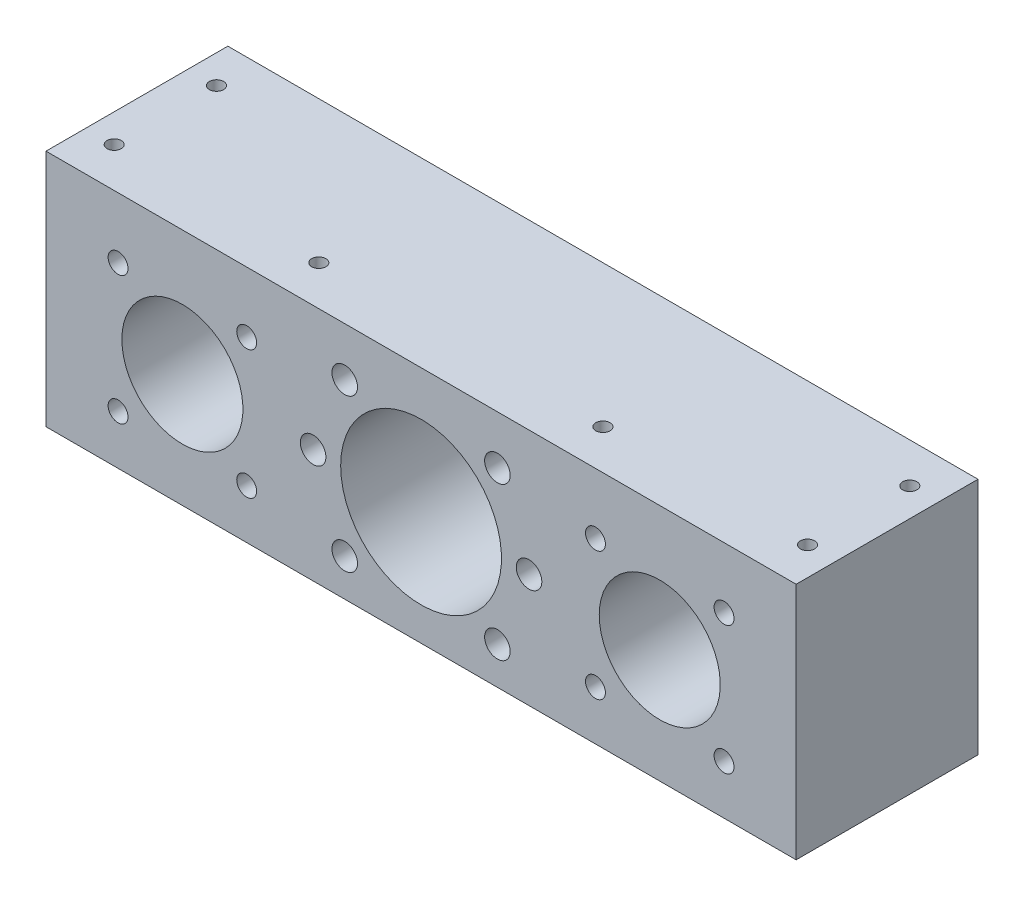
SolidWorks part; units mm, degrees
ref_plane "前视基准面" through (0, 0, 0) normal (0, 0, 1) x (1, 0, 0)
ref_plane "上视基准面" through (0, 0, 0) normal (0, 1, 0) x (1, 0, 0)
ref_plane "右视基准面" through (0, 0, 0) normal (1, 0, 0) x (0, 0, -1)
sketch "草图1" plane through (0, 0, 0) normal (0, 0, 1) x (1, 0, 0)
  line L1 (-66, 22) -> (66, 22)
  line L2 (-66, 22) -> (-66, -20)
  line L3 (-66, -20) -> (66, -20)
  line L4 (66, 22) -> (66, -20)
  dimension "D1" = 42
  dimension "D2" = 132
  dimension "D3" = 66
  dimension "D4" = 22
extrude "凸台-拉伸1" add sketch "草图1" along normal blind 32
sketch "草图2" plane through (0, 0, 0) normal (0, 0, -1) x (-1, 0, 0)
  circle A0 centre (0, 0) radius 14.15
  dimension "D1" = 28.3
extrude "切除-拉伸1" cut sketch "草图2" against normal blind 32
sketch "草图3" plane through (0, 0, 0) normal (0, 0, -1) x (-1, 0, 0)
  circle A0 centre (-42, 0) radius 10.65
  circle A1 centre (42, 0) radius 10.65
  dimension "D1" = 21.3
  dimension "D2" = 21.3
  dimension "D3" = 42
  dimension "D4" = 42
extrude "切除-拉伸2" cut sketch "草图3" against normal blind 32
sketch "草图6" plane through (0, 0, 32) normal (0, 0, 1) x (1, 0, 0)
  line L0 (25.1918, 8.3272) -> (27.1146, 8.7921)
  line L1 (27.1146, 8.7921) -> (27.6978, 8.9182)
  line L2 (27.6978, 8.9182) -> (28.2849, 9.0955)
  line L3 (28.2849, 9.0955) -> (28.8996, 9.328)
  line L4 (28.8996, 9.328) -> (29.1478, 9.4265)
  line L5 (29.1478, 9.4265) -> (29.8177, 9.659)
  line L6 (29.8177, 9.659) -> (30.2984, 9.328)
  line L7 (30.2984, 9.328) -> (30.8303, 8.8276)
  line L8 (30.59, 7.7716) -> (28.0209, 7.4603)
  line L9 (28.0209, 7.4603) -> (24.8095, 6.9875)
  line L10 (24.8095, 6.9875) -> (20.4003, 6.3097)
  line L11 (20.4003, 6.3097) -> (19.3207, 6.1285)
  line L12 (19.3207, 6.1285) -> (18.4696, 5.9472)
  line L13 (18.4696, 5.9472) -> (17.8707, 5.8172)
  line L14 (17.8707, 5.8172) -> (17.4924, 5.7344)
  line L15 (17.4924, 5.7344) -> (16.4009, 5.4035)
  line L16 (15.8414, 5.7226) -> (15.2976, 6.2427)
  line L17 (15.1006, 7.0544) -> (17.1299, 7.279)
  line L18 (17.1299, 7.279) -> (20.9677, 7.8267)
  line L19 (20.9677, 7.8267) -> (21.1336, 7.8433)
  line L20 (22.0543, 7.9656) -> (22.3508, 8.0119)
  line L21 (22.3508, 8.0119) -> (23.8757, 8.2484)
  line L22 (25.5858, 13.225) -> (25.6449, 14.0249)
  line L23 (25.6449, 14.0249) -> (26.4408, 14.2534)
  line L24 (26.4408, 14.2534) -> (27.489, 11.7513)
  line L25 (19.0409, 3.7879) -> (21.6061, 4.4302)
  line L26 (21.6061, 4.4302) -> (21.8661, 5.037)
  line L27 (22.9103, 5.0725) -> (23.4186, 4.4381)
  line L28 (23.6353, 3.7091) -> (23.2255, 3.1851)
  line L29 (23.1783, 2.2827) -> (23.1783, -5.9171)
  line L30 (21.5076, -10.8346) -> (21.1175, -10.0544)
  line L31 (21.1175, -10.0544) -> (20.5461, -9.0181)
  line L32 (20.5461, -9.0181) -> (19.3956, -6.9376)
  line L33 (19.3956, -6.9376) -> (19.829, -6.3938)
  line L34 (19.829, -6.3938) -> (21.6218, -8.1591)
  line L35 (21.7203, -6.3584) -> (21.7203, -3.4525)
  line L36 (21.7203, 3.126) -> (19.2892, 2.5388)
  line L37 (19.2892, 2.5388) -> (19.2892, 0.5214)
  line L38 (21.0032, 1.1755) -> (21.7203, 0.5627)
  line L39 (21.212, -0.373) -> (20.684, -0.4361)
  line L40 (20.684, -0.4361) -> (19.2892, -0.7316)
  line L41 (19.2892, -0.7316) -> (19.2892, -2.6111)
  line L42 (21.0465, -1.9571) -> (21.7203, -2.5391)
  line L43 (21.3066, -3.5332) -> (20.6131, -3.6356)
  line L44 (20.6131, -3.6356) -> (20.0221, -3.742)
  line L45 (20.0221, -3.742) -> (19.2892, -3.872)
  line L46 (19.2892, -3.872) -> (19.2852, -8.1394)
  line L47 (19.2852, -8.1394) -> (19.2576, -9.6604)
  line L48 (19.2576, -9.6604) -> (19.2025, -10.6809)
  line L49 (18.0322, -11.1892) -> (17.7918, -10.6809)
  line L50 (17.7918, -10.6809) -> (17.5357, -10.015)
  line L51 (17.8273, -5.5782) -> (17.8273, 1.9675)
  line L52 (17.7761, 3.654) -> (17.6736, 4.2489)
  line L53 (17.6736, 4.2489) -> (17.5673, 5.1473)
  line L54 (17.5673, 5.1473) -> (18.4105, 5.431)
  line L55 (18.4105, 5.431) -> (19.0409, 3.7879)
  line L56 (19.5847, 13.2092) -> (20.4437, 12.5197)
  line L57 (20.4437, 12.5197) -> (20.9441, 11.9404)
  line L58 (20.9441, 11.9404) -> (21.4169, 11.3651)
  line L59 (21.4169, 11.3651) -> (22.0001, 10.6559)
  line L60 (22.3863, 9.4108) -> (22.1735, 8.3626)
  line L61 (21.1293, 7.8543) -> (20.9205, 8.4611)
  line L62 (20.9205, 8.4611) -> (20.5028, 9.5999)
  line L63 (20.5028, 9.5999) -> (20.227, 10.2855)
  line L64 (20.227, 10.2855) -> (19.6556, 11.4597)
  line L65 (19.6556, 11.4597) -> (19.1079, 12.6852)
  line L66 (19.1079, 12.6852) -> (19.5847, 13.2092)
  line L67 (24.0412, 4.3199) -> (24.7032, 4.6233)
  line L68 (24.7032, 4.6233) -> (26.1296, 2.6413)
  line L69 (25.7119, 1.1322) -> (25.7119, -3.6435)
  line L70 (24.5337, -5.1448) -> (24.3249, -4.7507)
  line L71 (24.3249, -4.7507) -> (24.1082, -4.27)
  line L72 (24.0451, -3.7814) -> (24.183, -3.2771)
  line L73 (24.3288, -2.162) -> (24.3012, 0.4741)
  line L74 (24.3012, 0.4741) -> (24.3012, 1.7981)
  line L75 (24.4628, -6.9416) -> (26.5709, -8.4152)
  line L76 (26.8349, -6.5948) -> (26.8349, 2.2276)
  line L77 (26.7048, 5.3128) -> (26.5236, 6.3846)
  line L78 (26.5236, 6.3846) -> (27.0831, 6.8653)
  line L79 (27.0831, 6.8653) -> (28.7656, 4.8439)
  line L80 (28.2967, 2.3852) -> (28.2967, -8.1867)
  line L81 (28.21, -9.885) -> (28.1312, -10.6691)
  line L82 (26.7679, -11.1656) -> (26.3778, -10.5785)
  line L83 (26.3778, -10.5785) -> (25.771, -9.7234)
  line L84 (25.771, -9.7234) -> (24.6913, -8.3404)
  line L85 (24.6913, -8.3404) -> (24.1476, -7.5405)
  line L86 (24.1476, -7.5405) -> (24.4628, -6.9416)
  line L87 (21.7203, 0.5627) -> (21.7203, 3.126)
  line L88 (21.7203, -2.5391) -> (21.7203, -0.2932)
  line L89 (21.7203, -6.3584) -> (21.6218, -8.1591)
  line L90 (26.8349, -6.5948) -> (26.5709, -8.4152)
  spline S0 degree 3 poles (30.8303, 8.8276) (30.9744, 8.6945) (31.1391, 8.499) (31.2842, 8.2301) (31.2861, 8.0724) (31.1985, 7.9521) (30.9693, 7.8226) (30.7475, 7.7999) (30.59, 7.7716) knots 0 0 0 0 0.347386 0.457637 0.53741 0.613513 0.710465 1 1 1 1
  spline S1 degree 2 poles (16.4009, 5.4035) (16.0728, 5.4755) (15.8414, 5.7226) knots 0 0 0 1 1 1
  spline S2 degree 3 poles (15.2976, 6.2427) (15.214, 6.3213) (15.0998, 6.4262) (15.005, 6.5827) (14.956, 6.7793) (15.0657, 6.9388) (15.1006, 7.0544) knots 0 0 0 0 0.367731 0.487674 0.578039 1 1 1 1
  spline S3 degree 3 poles (23.8757, 8.2484) (24.0035, 8.5899) (24.2006, 9.0762) (24.4317, 9.705) (24.5935, 10.1078) (24.7245, 10.4742) (24.8484, 10.7943) (24.9507, 11.076) (25.0622, 11.386) (25.1843, 11.7218) (25.3016, 12.0834) (25.3954, 12.3954) (25.456, 12.6599) (25.5036, 12.8729) (25.5426, 13.0561) (25.5699, 13.1676) (25.5858, 13.225) knots 0 0 0 0 0.207633 0.298753 0.381388 0.45474 0.520301 0.576848 0.625344 0.707897 0.780266 0.841801 0.893317 0.934687 0.966079 1 1 1 1
  spline S4 degree 3 poles (27.489, 11.7513) (27.3166, 11.6039) (27.0782, 11.39) (26.8064, 11.0984) (26.6694, 10.9273) (26.563, 10.7652) (26.4556, 10.589) (26.3203, 10.3536) (26.1489, 10.0626) (25.9535, 9.7103) (25.627, 9.1276) (25.372, 8.6587) (25.1918, 8.3272) knots 0 0 0 0 0.163792 0.230902 0.287626 0.321818 0.370773 0.436645 0.517807 0.614614 0.727539 1 1 1 1
  spline S5 degree 3 poles (21.8661, 5.037) (21.9316, 5.1603) (22.0667, 5.3139) (22.311, 5.3773) (22.5853, 5.3094) (22.7721, 5.1729) (22.9103, 5.0725) knots 0 0 0 0 0.341138 0.451231 0.589089 1 1 1 1
  spline S6 degree 3 poles (23.4186, 4.4381) (23.4911, 4.3284) (23.591, 4.1866) (23.6748, 4.0045) (23.6983, 3.867) (23.6572, 3.7728) (23.6353, 3.7091) knots 0 0 0 0 0.489758 0.643143 0.741981 1 1 1 1
  spline S7 degree 3 poles (23.2255, 3.1851) (23.2035, 3.1054) (23.1864, 2.9905) (23.1819, 2.8278) (23.1741, 2.6085) (23.1812, 2.4219) (23.1783, 2.2827) knots 0 0 0 0 0.273514 0.382334 0.538971 1 1 1 1
  spline S8 degree 3 poles (23.1783, -5.9171) (23.1805, -6.0393) (23.1743, -6.2375) (23.1709, -6.5239) (23.1627, -6.7853) (23.1499, -7.0781) (23.1381, -7.4025) (23.1275, -7.7586) (23.1061, -8.2551) (23.0808, -8.8412) (23.0384, -9.4667) (22.99, -9.973) (22.9308, -10.3688) (22.8661, -10.6751) (22.8008, -10.9145) (22.7302, -11.0985) (22.6203, -11.2678) (22.4267, -11.3971) (22.2013, -11.4735) (21.986, -11.4379) (21.7293, -11.2415) (21.6053, -11.0036) (21.5076, -10.8346) knots 0 0 0 0 0.053419 0.086736 0.125234 0.16777 0.214897 0.267191 0.323523 0.432196 0.523735 0.597629 0.65457 0.698614 0.734431 0.763016 0.784521 0.821511 0.862616 0.885373 0.913888 1 1 1 1
  spline S10 degree 3 poles (19.2892, 0.5214) (19.6067, 0.617) (20.1939, 0.7958) (20.7529, 1.0491) (21.0032, 1.1755) knots 0 0 0 0 0.541942 1 1 1 1
  spline S11 degree 3 poles (21.7203, -0.2932) (21.553, -0.3312) (21.3825, -0.3562) (21.212, -0.373) knots 0.675613 0.675613 0.675613 0.675613 1 1 1 1
  spline S12 degree 3 poles (19.2892, -2.6111) (19.5523, -2.5165) (20.1398, -2.303) (20.7236, -2.0796) (21.0465, -1.9571) knots 0 0 0 0 0.447378 1 1 1 1
  spline S13 degree 3 poles (21.7203, -3.4525) (21.5845, -3.4885) (21.4454, -3.5118) (21.3066, -3.5332) knots 0.741321 0.741321 0.741321 0.741321 1 1 1 1
  spline S14 degree 3 poles (19.2025, -10.6809) (19.1886, -10.8452) (19.1538, -11.0959) (18.976, -11.363) (18.8226, -11.5168) (18.6299, -11.612) (18.3019, -11.5526) (18.1418, -11.3256) (18.0322, -11.1892) knots 0 0 0 0 0.265053 0.383706 0.501207 0.607272 0.707999 1 1 1 1
  spline S15 degree 3 poles (17.5357, -10.015) (17.4773, -9.8851) (17.396, -9.6923) (17.4488, -9.4533) (17.487, -9.2926) (17.5511, -9.0823) (17.6299, -8.8714) (17.6845, -8.644) (17.7216, -8.4016) (17.7573, -8.0928) (17.7829, -7.7181) (17.8013, -7.2766) (17.8249, -6.5569) (17.824, -5.9827) (17.8273, -5.5782) knots 0 0 0 0 0.100293 0.125218 0.1622 0.210716 0.271682 0.312278 0.366447 0.435254 0.519605 0.616976 0.730077 1 1 1 1
  spline S16 degree 3 poles (17.8273, 1.9675) (17.8245, 2.2893) (17.8242, 2.852) (17.7974, 3.4141) (17.7761, 3.654) knots 0 0 0 0 0.572057 1 1 1 1
  spline S17 degree 3 poles (22.0001, 10.6559) (22.1102, 10.5083) (22.2565, 10.3122) (22.3955, 10.0631) (22.4717, 9.7977) (22.3911, 9.577) (22.3863, 9.4108) knots 0 0 0 0 0.402738 0.535126 0.621583 1 1 1 1
  spline S18 degree 3 poles (22.1735, 8.3626) (22.1491, 8.2261) (22.1134, 8.0907) (22.0543, 7.9656) knots 0 0 0 0 0.260339 0.260339 0.260339 0.260339
  spline S19 degree 3 poles (26.1296, 2.6413) (25.9893, 2.4287) (25.7744, 1.9381) (25.7133, 1.4066) (25.7119, 1.1322) knots 0 0 0 0 0.480509 1 1 1 1
  spline S20 degree 3 poles (25.7119, -3.6435) (25.7149, -3.9568) (25.6903, -4.395) (25.5685, -4.9189) (25.4692, -5.1684) (25.3634, -5.3179) (25.2774, -5.3957) (25.176, -5.4398) (25.0643, -5.4396) (24.9435, -5.4151) (24.7524, -5.332) (24.6247, -5.2208) (24.5337, -5.1448) knots 0 0 0 0 0.351023 0.487127 0.600936 0.648243 0.690945 0.72914 0.768831 0.813774 0.866434 1 1 1 1
  spline S21 degree 2 poles (24.1082, -4.27) (24.0242, -4.0322) (24.0451, -3.7814) knots 0 0 0 1 1 1
  spline S22 degree 3 poles (24.183, -3.2771) (24.2346, -3.136) (24.2915, -2.7631) (24.3344, -2.3896) (24.3288, -2.162) knots 0 0 0 0 0.397178 1 1 1 1
  spline S23 degree 3 poles (24.3012, 1.7981) (24.2834, 2.0607) (24.2661, 2.4146) (24.2238, 2.8937) (24.1644, 3.4729) (24.0895, 3.9587) (24.0412, 4.3199) knots 0 0 0 0 0.311368 0.418968 0.568917 1 1 1 1
  spline S25 degree 3 poles (26.8349, 2.2276) (26.8252, 2.6714) (26.8405, 3.2773) (26.8128, 4.0034) (26.7983, 4.3818) (26.7785, 4.6801) (26.7481, 4.9823) (26.725, 5.1886) (26.7048, 5.3128) knots 0 0 0 0 0.430919 0.587813 0.705214 0.798498 0.877911 1 1 1 1
  spline S26 degree 3 poles (28.7656, 4.8439) (28.6653, 4.6267) (28.5159, 4.3304) (28.3951, 3.9506) (28.3364, 3.7262) (28.323, 3.4858) (28.2956, 3.0387) (28.302, 2.662) (28.2967, 2.3852) knots 0 0 0 0 0.283364 0.389307 0.470566 0.556221 0.672708 1 1 1 1
  spline S27 degree 3 poles (28.2967, -8.1867) (28.2987, -8.4879) (28.2688, -9.0542) (28.2328, -9.62) (28.21, -9.885) knots 0 0 0 0 0.530905 1 1 1 1
  spline S28 degree 3 poles (28.1312, -10.6691) (28.0976, -10.9143) (28.0676, -11.2453) (27.8673, -11.598) (27.6818, -11.6953) (27.5159, -11.7134) (27.3747, -11.7227) (27.2626, -11.7209) (27.164, -11.7037) (27.0806, -11.6324) (26.9333, -11.4643) (26.8478, -11.2859) (26.7679, -11.1656) knots 0 0 0 0 0.315764 0.418272 0.498355 0.571215 0.629844 0.678372 0.714475 0.753944 0.814359 1 1 1 1
  spline S29 degree 2 poles (21.1336, 7.8433) (21.1313, 7.8488) (21.1293, 7.8543) knots 0.992819 0.992819 0.992819 1 1 1
extrude "切除-拉伸6" [suppressed] cut sketch "草图6" against normal blind 1.5
sketch "草图7" plane through (0, 0, 0) normal (0, 0, -1) x (-1, 0, 0)
  line L0 (-24, 0) -> (-21.2486, 0)
  line L1 (0, 0) -> (0, 24)
  line L2 (-13.2665, 20) -> (0, 20)
  line L3 (-13.2665, -20) -> (13.2665, -20)
  line L4 (0, 0) -> (-11.844, 11.844)
  line L5 (0, 0) -> (-11.844, -11.844)
  line L6 (0, 0) -> (11.844, -11.844)
  line L7 (0, 0) -> (11.844, 11.844)
  line L8 (21.2485, 0) -> (24, 0)
  line L9 (-16.7486, 0) -> (16.7485, 0)
  line L10 (25.8, 16.2) -> (52.0763, -10.0763)
  line L11 (25.8, -16.2) -> (58.2, -16.2)
  line L12 (25.8, -16.2) -> (25.8, 16.2)
  line L13 (25.8, 16.2) -> (58.2, 16.2)
  line L14 (58.2, -16.2) -> (58.2, 16.2)
  line L15 (25.8, -16.2) -> (29.4489, -12.5511) construction
  line L16 (25.8, 16.2) -> (58.2, -16.2) construction
  line L17 (-58.2, 16.2) -> (-25.8, 16.2)
  line L18 (-58.2, 16.2) -> (-58.2, -16.2)
  line L19 (-58.2, -16.2) -> (-25.8, -16.2)
  line L20 (-25.8, 16.2) -> (-25.8, -16.2)
  line L21 (-58.2, 16.2) -> (-25.8, -16.2) construction
  line L22 (-58.2, -16.2) -> (-25.8, 16.2) construction
  line L23 (25.8, -16.2) -> (29.4489, -12.5511)
  line L24 (-25.8, 16.2) -> (-29.4489, 12.5511)
  line L25 (-58.2, 16.2) -> (-54.5511, 12.5511)
  line L26 (31.9237, -10.0763) -> (52.0763, 10.0763)
  line L27 (31.9237, -10.0763) -> (58.2, 16.2) construction
  line L28 (54.5511, 12.5511) -> (58.2, 16.2)
  line L29 (54.5511, -12.5511) -> (58.2, -16.2)
  line L30 (-52.0763, 10.0763) -> (-31.9237, -10.0763)
  line L31 (-31.9237, 10.0763) -> (-52.0763, -10.0763)
  line L32 (-54.5511, -12.5511) -> (-58.2, -16.2)
  line L33 (-29.4489, -12.5511) -> (-25.8, -16.2)
  arc A0 (-24, 0) -> (13.2665, 20) centre (0, 0) ccw
  circle A2 centre (-18.9986, 0) radius 2.25
  circle A3 centre (18.9985, 0) radius 2.25
  circle A4 centre (13.435, 13.435) radius 2.25
  circle A5 centre (13.435, -13.435) radius 2.25
  circle A6 centre (-13.435, -13.435) radius 2.25
  circle A7 centre (-13.435, 13.435) radius 2.25
  circle A9 centre (-53.3137, 11.3137) radius 1.75
  circle A10 centre (-30.6863, 11.3137) radius 1.75
  circle A11 centre (-30.6863, -11.3137) radius 1.75
  circle A12 centre (-53.3137, -11.3137) radius 1.75
  circle A13 centre (30.6863, 11.3137) radius 1.75
  circle A14 centre (30.6863, -11.3137) radius 1.75
  circle A15 centre (53.3137, -11.3137) radius 1.75
  circle A16 centre (53.3137, 11.3137) radius 1.75
  point P23 (42, 0)
  point P36 (-42, 0)
  dimension "D1" = 48
  dimension "D4" = 32.4
  dimension "D5" = 4.5
  dimension "D6" = 4.5
  dimension "D11" = 4.5
  dimension "D12" = 4.5
  dimension "D13" = 4.5
  dimension "D14" = 4.5
  dimension "D20" = 3.5
  dimension "D21" = 3.5
  dimension "D22" = 3.5
  dimension "D23" = 3.5
  dimension "D24" = 3.5
  dimension "D25" = 3.5
  dimension "D26" = 3.5
  dimension "D27" = 3.5
  dimension "D2" = 20
  dimension "D3" = 20
  dimension "D7" = 45
  dimension "D8" = 45
  dimension "D9" = 45
  dimension "D10" = 45
  dimension "D15" = 32.4
  dimension "D16" = 32.4
  dimension "D17" = 32.4
extrude "切除-拉伸8" cut sketch "草图7" against normal blind 32 contours A9 | A12 | A11 | A7 | A2 | A6 | A5 | A3 | A4 | L10 A13 | A14 | L10 A13 | A15 | A16 | A10
sketch "草图8" plane through (0, 0, 0) normal (0, 0, -1) x (-1, 0, 0)
  line L0 (-13.4172, 20.2) -> (13.4172, 20.2)
  line L1 (0, 0) -> (-24.25, 0)
  line L2 (-24.25, 0) -> (24.25, 0)
  line L3 (-13.7136, -20) -> (13.7136, -20)
  arc A0 (-13.4172, 20.2) -> (-13.7136, -20) centre (0, 0) ccw
  arc A1 (13.7136, -20) -> (13.4172, 20.2) centre (0, 0) ccw
  circle M6 centre (13.435, 13.435) radius 2.25
  circle M7 centre (18.9985, 0) radius 2.25
  circle M8 centre (13.435, -13.435) radius 2.25
  circle M9 centre (-13.435, -13.435) radius 2.25
  circle M10 centre (-18.9986, 0) radius 2.25
  circle M11 centre (-13.435, 13.435) radius 2.25
  circle M17 centre (0, 0) radius 14.15
  line M21 (-66, -20) -> (66, -20)
  dimension "D1" = 48.5
  dimension "D2" = 20.2
  dimension "D3" = 20
extrude "切除-拉伸9" cut sketch "草图8" against normal blind 10 contours L2 A1 L0 A0 L1 M10 M17 M7 M11 M6 | A1 L2 L1 A0 M21 M7 M17 M10 M9 M8
sketch "草图9" plane through (0, 0, 0) normal (0, 0, -1) x (-1, 0, 0)
  line L1 (28.3069, 16.25) -> (55.6931, 16.25)
  line L2 (25.75, 13.6931) -> (25.75, -13.6931)
  line L3 (28.3069, -16.25) -> (55.6931, -16.25)
  line L4 (58.25, 13.6931) -> (58.25, -13.6931)
  line L5 (25.75, 16.25) -> (58.25, -16.25) construction
  line L6 (25.75, -16.25) -> (58.25, 16.25) construction
  line L7 (-55.6931, 16.25) -> (-28.3069, 16.25)
  line L8 (-58.25, 13.6931) -> (-58.25, -13.6931)
  line L9 (-55.6931, -16.25) -> (-28.3069, -16.25)
  line L10 (-25.75, 13.6931) -> (-25.75, -13.6931)
  line L11 (-58.25, 16.25) -> (-25.75, -16.25) construction
  line L12 (-58.25, -16.25) -> (-25.75, 16.25) construction
  arc A0 (25.75, -13.6931) -> (28.3069, -16.25) centre (42, 0) ccw
  arc A1 (28.3069, 16.25) -> (25.75, 13.6931) centre (42, 0) ccw
  arc A2 (58.25, 13.6931) -> (55.6931, 16.25) centre (42, 0) ccw
  arc A3 (55.6931, -16.25) -> (58.25, -13.6931) centre (42, 0) ccw
  arc A4 (-55.6931, 16.25) -> (-58.25, 13.6931) centre (-42, 0) ccw
  arc A5 (-25.75, 13.6931) -> (-28.3069, 16.25) centre (-42, 0) ccw
  arc A6 (-28.3069, -16.25) -> (-25.75, -13.6931) centre (-42, 0) ccw
  arc A7 (-58.25, -13.6931) -> (-55.6931, -16.25) centre (-42, 0) ccw
  point P0 (42, 0)
  point P15 (-42, 0)
  dimension "D3" = 42.5
  dimension "D6" = 42.5
  dimension "D1" = 32.5
  dimension "D2" = 32.5
  dimension "D4" = 32.5
  dimension "D5" = 32.5
extrude "切除-拉伸10" cut sketch "草图9" against normal blind 6
sketch "草图10" plane through (0, 22, 0) normal (0, 1, 0) x (1, 0, 0)
  line L0 (-66, -32) -> (66, -32) construction
  line L1 (66, -32) -> (66, 0) construction
  line L2 (-66, -32) -> (-66, 0) construction
  line L4 (-66, -16) -> (66, -16)
  line L5 (-66, -32) -> (-66, 0) construction
  line L6 (66, -32) -> (66, 0) construction
  circle A0 centre (25, -25) radius 1.25
  circle A1 centre (61, -25) radius 1.25
  circle A2 centre (-25, -25) radius 1.25
  circle A3 centre (-61, -25) radius 1.25
  circle A4 centre (61, -7) radius 1.25
  circle A5 centre (25, -7) radius 1.25
  circle A6 centre (-25, -7) radius 1.25
  circle A7 centre (-61, -7) radius 1.25
  dimension "D1" = 2.5
  dimension "D2" = 2.5
  dimension "D3" = 2.5
  dimension "D4" = 2.5
  dimension "D5" = 25
  dimension "D6" = 25
  dimension "D7" = 7
  dimension "D8" = 7
  dimension "D9" = 5
  dimension "D10" = 7
  dimension "D12" = 7
  dimension "D11" = 5
extrude "切除-拉伸26" cut sketch "草图10" against normal blind 10 contours A2 | A0 | A1 | A4 | A7 | A3
